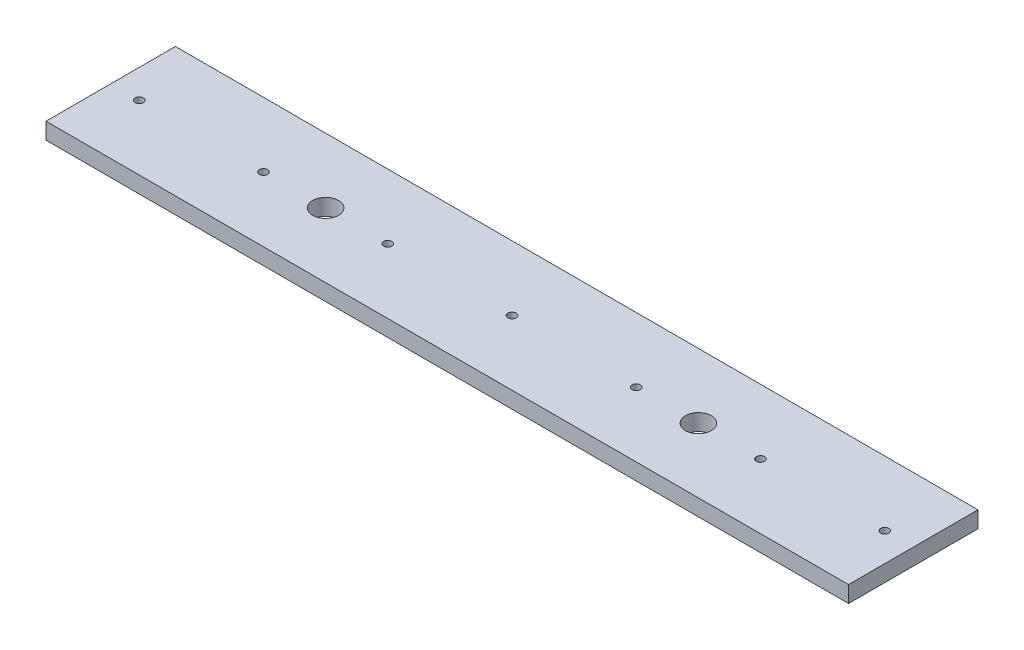
SolidWorks part; units mm, degrees
ref_plane "Alzado" through (0, 0, 0) normal (0, 0, 1) x (1, 0, 0)
ref_plane "Planta" through (0, 0, 0) normal (0, 1, 0) x (1, 0, 0)
ref_plane "Vista lateral" through (0, 0, 0) normal (1, 0, 0) x (0, 0, -1)
sketch "Croquis1" plane through (0, 0, 0) normal (0, 1, 0) x (1, 0, 0)
  line L1 (-155, -25) -> (155, -25)
  line L2 (-155, -25) -> (-155, 25)
  line L3 (-155, 25) -> (155, 25)
  line L4 (155, -25) -> (155, 25)
  line L5 (-155, -25) -> (155, 25) construction
  line L6 (-155, 25) -> (155, -25) construction
  point P0 (0, 0)
  dimension "D1" = 310
  dimension "50" = 50
extrude "Saliente-Extruir1" add sketch "Croquis1" along normal blind 6.35
sketch "Croquis2" plane through (0, 6.35, 0) normal (0, 1, 0) x (1, 0, 0)
  circle A0 centre (0, 0) radius 1.5875
  circle A1 centre (-144, 0) radius 1.5875
  circle A2 centre (144, 0) radius 1.5875
  circle A3 centre (48, 0) radius 1.5875
  circle A4 centre (96, 0) radius 1.5875
  circle A5 centre (-48, 0) radius 1.5875
  circle A6 centre (-96, 0) radius 1.5875
  circle A7 centre (-72, 0) radius 5
  circle A8 centre (72, 0) radius 5
  dimension "D1" = 48
  dimension "D7" = 10
  dimension "D8" = 10
  dimension "D2" = 48
  dimension "D3" = 48
  dimension "D4" = 48
  dimension "D5" = 48
  dimension "D6" = 48
  dimension "D9" = 24
  dimension "D10" = 24
extrude "Cortar-Extruir3" cut sketch "Croquis2" against normal through all
